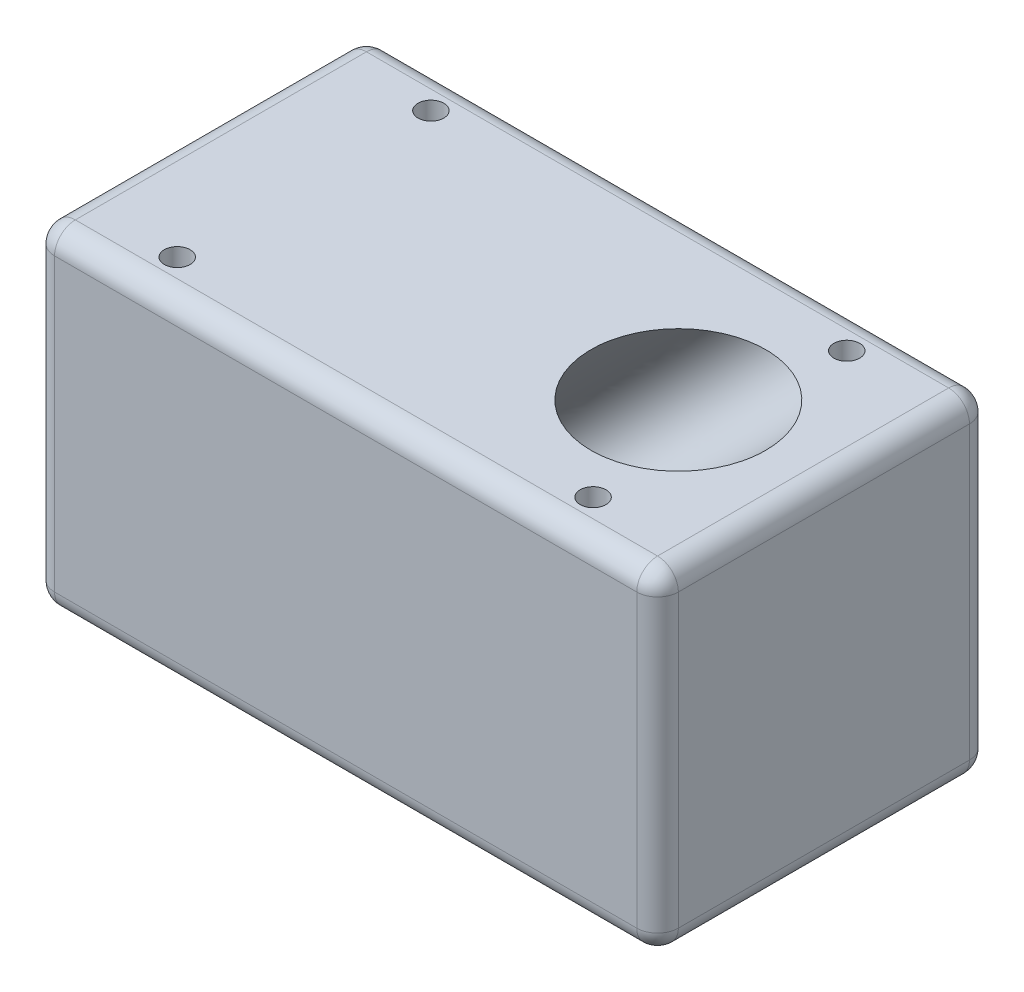
SolidWorks part; units mm, degrees
ref_plane "Front Plane" through (0, 0, 0) normal (0, 0, 1) x (1, 0, 0)
ref_plane "Top Plane" through (0, 0, 0) normal (0, 1, 0) x (1, 0, 0)
ref_plane "Right Plane" through (0, 0, 0) normal (1, 0, 0) x (0, 0, -1)
sketch "Sketch1" plane through (0, 0, 0) normal (0, 1, 0) x (1, 0, 0)
  line L1 (-37.5, -20) -> (37.5, -20)
  line L2 (-37.5, -20) -> (-37.5, 20)
  line L3 (-37.5, 20) -> (37.5, 20)
  line L4 (37.5, -20) -> (37.5, 20)
  line L5 (-37.5, -20) -> (37.5, 20) construction
  line L6 (-37.5, 20) -> (37.5, -20) construction
  point P0 (0, 0)
  dimension "D1" = 75
  dimension "D2" = 40
extrude "Boss-Extrude1" add sketch "Sketch1" along normal blind 40
sketch "Sketch2" plane through (-37.5, 0, 0) normal (-1, 0, 0) x (0, 0, 1)
  circle A0 centre (0, 17.5) radius 10.5
  dimension "D1" = 21
extrude "Cut-Extrude1" cut sketch "Sketch2" against normal blind 30
sketch "Sketch3" plane through (0, 40, 0) normal (0, 1, 0) x (1, 0, 0)
  circle A0 centre (-25, 15.25) radius 1.55
  circle A1 centre (25, 15.25) radius 1.55
  circle A3 centre (-25, -15.25) radius 1.55
  circle A4 centre (25, -15.25) radius 1.55
  dimension "D1" = 50
  dimension "D2" = 30.5
  dimension "D3" = 3.1
  dimension "D4" = 3.1
  dimension "D5" = 3.1
  dimension "D6" = 3.1
  dimension "D7" = 15.25
  dimension "D8" = 25
extrude "Cut-Extrude2" cut sketch "Sketch3" against normal up to surface (40 mm away) up to face at (0, 0, 0)
fillet "Fillet1" radius 2.5 13 edges at (37.5, 40, 0) (0, 40, 20) (37.5, 20, 20) (0, 0, 20) (37.5, 0, 0) (37.5, 20, -20) (0, 40, -20) (0, 0, -20) (-37.5, 20, -20) (-37.5, 40, 0) (-37.5, 20, 20) (-37.5, 0, 0) (-37.5, 17.5, 10.5)
sketch "Sketch4" plane through (0, 40, 0) normal (0, 1, 0) x (1, 0, 0)
  circle A1 centre (20, 0) radius 10.5
  dimension "D1" = 21
  dimension "D2" = 20
sketch "Sketch6" plane through (0, 0, 0) normal (0, 1, 0) x (1, 0, 0)
  circle A0 centre (-20, 0) radius 10.5
  dimension "D1" = 21
  dimension "D2" = 20
loft "Cut-Loft1" cut profiles "Sketch6", "Sketch4"
